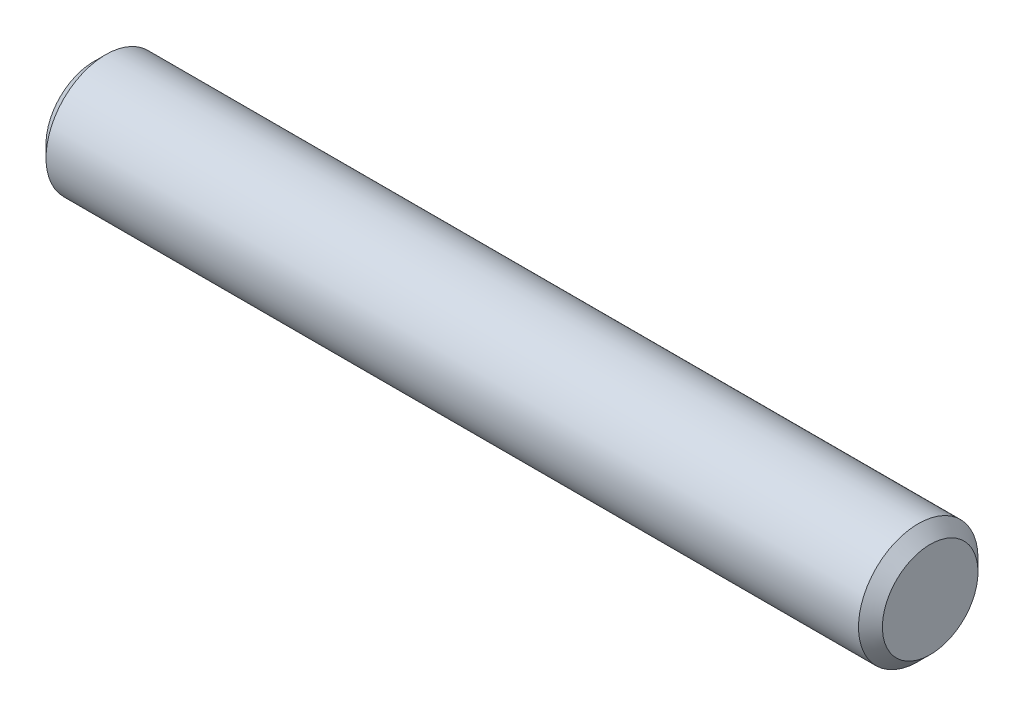
SolidWorks part; units mm, degrees
ref_plane "Front" through (0, 0, 0) normal (0, 0, 1) x (1, 0, 0)
ref_plane "Top" through (0, 0, 0) normal (0, 1, 0) x (1, 0, 0)
ref_plane "Right" through (0, 0, 0) normal (1, 0, 0) x (0, 0, -1)
sketch "Sketch1" plane through (0, 0, 0) normal (0, 0, 1) x (1, 0, 0)
  line L0 (-22.225, 0) -> (22.225, 0) construction
  line L1 (22.225, 3.175) -> (22.225, -3.175) construction
  line L2 (-22.225, 3.175) -> (-22.225, -3.175) construction
  dimension "Length" = 44.45
  dimension "Diameter" = 6.35
sketch "Sketch2" plane through (0, 0, 0) normal (1, 0, 0) x (0, 0, -1)
  circle A0 centre (0, 0) radius 3.175
extrude "Extrude1" add sketch "Sketch2" against normal up to vertex (22.225 mm away) and the other way up to vertex (22.225 mm away) up to point (-22.225, 3.175, 0) other way up to point (22.225, 3.175, 0)
chamfer "Chamfer1" distance 0.635 angle 45 2 edges at (22.225, 0, -3.175) (-22.225, 0, -3.175)
equation "\"D1@Chamfer1\" = \"Diameter@Sketch1\"*.1"
